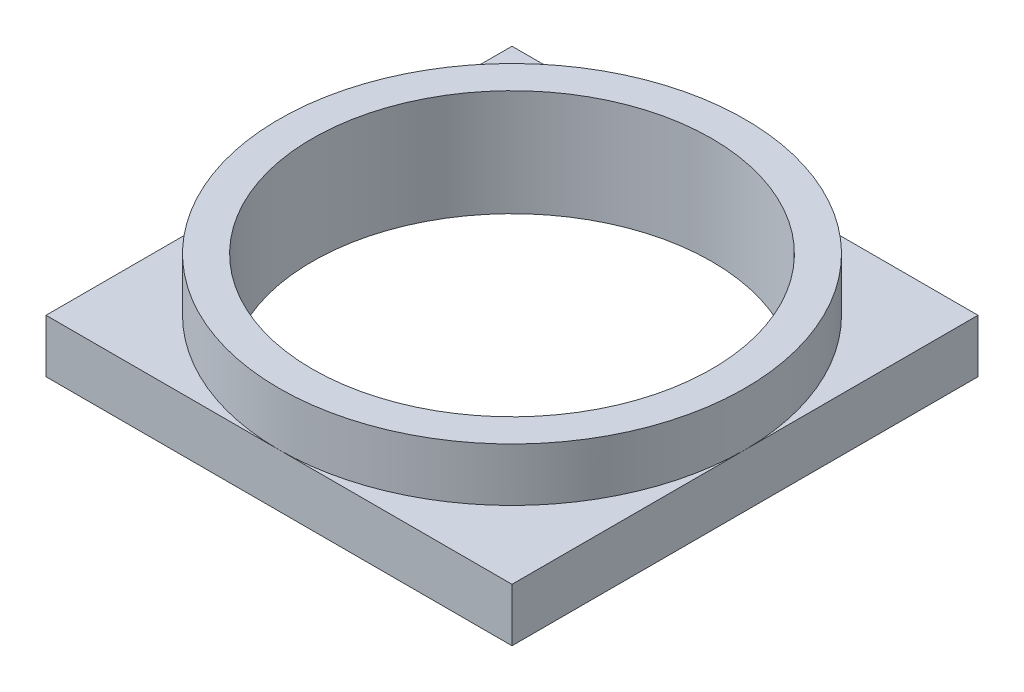
SolidWorks part; units mm, degrees
ref_plane "Front Plane" through (0, 0, 0) normal (0, 0, 1) x (1, 0, 0)
ref_plane "Top Plane" through (0, 0, 0) normal (0, 1, 0) x (1, 0, 0)
ref_plane "Right Plane" through (0, 0, 0) normal (1, 0, 0) x (0, 0, -1)
sketch "Sketch1" plane through (0, 0, 0) normal (0, 1, 0) x (1, 0, 0)
  line L1 (-7, -7) -> (7, -7)
  line L2 (-7, -7) -> (-7, 7)
  line L3 (-7, 7) -> (7, 7)
  line L4 (7, -7) -> (7, 7)
  line L5 (-7, -7) -> (7, 7) construction
  line L6 (-7, 7) -> (7, -7) construction
  point P0 (0, 0)
  dimension "D1" = 14
  dimension "D2" = 14
extrude "Boss-Extrude1" add sketch "Sketch1" along normal blind 1.6
sketch "Sketch2" plane through (0, 1.6, 0) normal (0, 1, 0) x (1, 0, 0)
  circle A0 centre (0, 0) radius 6
  circle A1 centre (0, 0) radius 7
  dimension "D1" = 12
extrude "Boss-Extrude2" add sketch "Sketch2" along normal blind 1.6
sketch "Sketch3" plane through (0, 1.6, 0) normal (0, 1, 0) x (1, 0, 0)
  circle A0 centre (0, 0) radius 6
  dimension "D1" = 12
extrude "Cut-Extrude1" cut sketch "Sketch3" against normal through all
